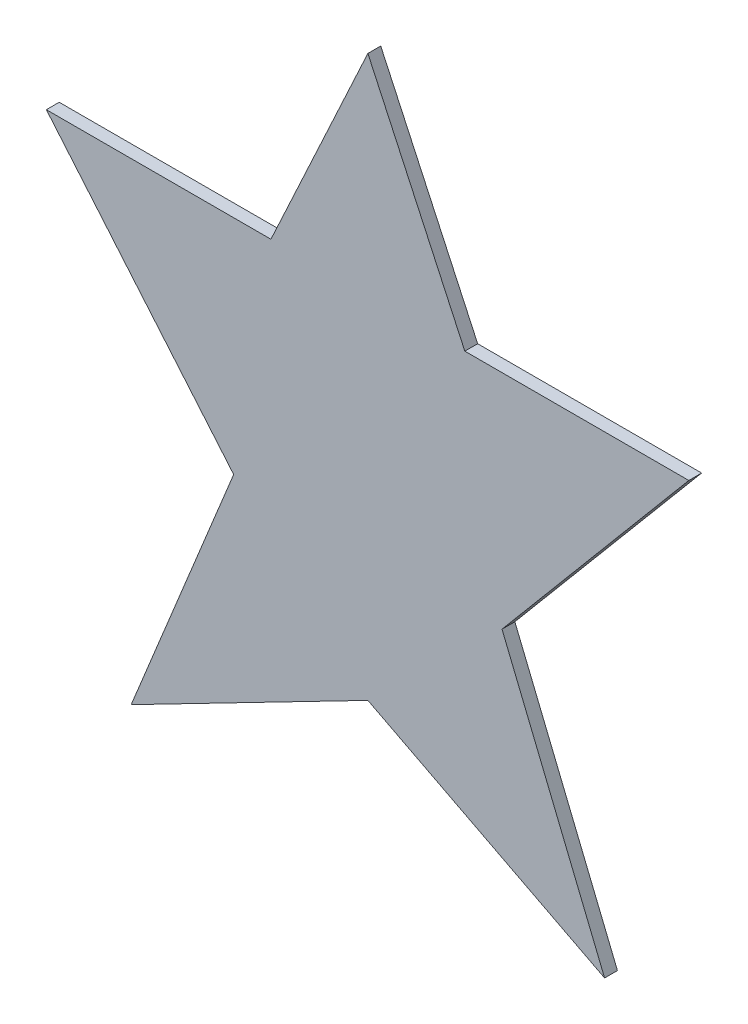
SolidWorks part; units mm, degrees
ref_plane "Alzado" through (0, 0, 0) normal (0, 0, 1) x (1, 0, 0)
ref_plane "Planta" through (0, 0, 0) normal (0, 1, 0) x (1, 0, 0)
ref_plane "Vista lateral" through (0, 0, 0) normal (1, 0, 0) x (0, 0, -1)
sketch "Model" plane through (0, 0, 0) normal (0, 0, 1) x (1, 0, 0)
  line L0 (9.8181, -1.4027) -> (11.5621, -1.4027)
  line L1 (11.5621, -1.4027) -> (10.1077, -3.1328)
  line L2 (10.1077, -3.1328) -> (10.9066, -5.0856)
  line L3 (10.9066, -5.0856) -> (9.0633, -4.1352)
  line L4 (9.0633, -4.1352) -> (7.22, -5.0857)
  line L5 (7.22, -5.0857) -> (8.0182, -3.1345)
  line L6 (9.8181, -1.4027) -> (9.0633, 0.2275)
  line L7 (9.0633, 0.2275) -> (8.3083, -1.403)
  line L8 (8.3083, -1.403) -> (6.5596, -1.4036)
  line L9 (6.5596, -1.4036) -> (8.0182, -3.1345)
extrude "Saliente-Extruir1" add sketch "Model" along normal blind 0.1
